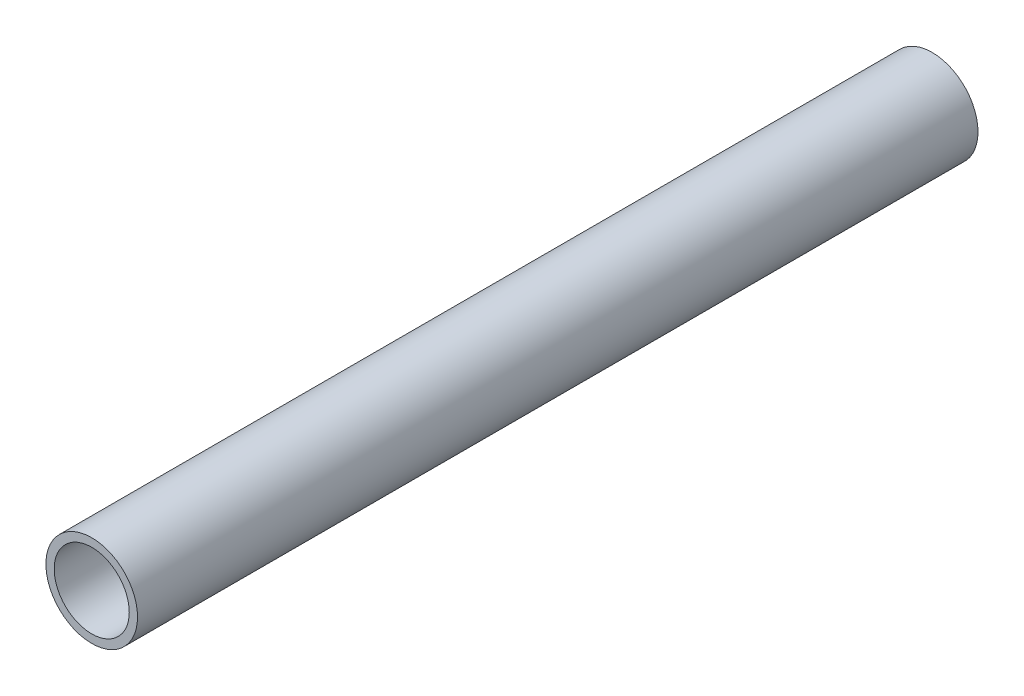
SolidWorks part; units mm, degrees
material "Thornel Mat VMA"
ref_plane "Płaszczyzna XY" through (0, 0, 0) normal (0, 0, 1) x (1, 0, 0)
ref_plane "Płaszczyzna XZ" through (0, 0, 0) normal (0, 1, 0) x (1, 0, 0)
ref_plane "Płaszczyzna YZ" through (0, 0, 0) normal (1, 0, 0) x (0, 0, -1)
sketch "Szkic1" plane through (0, 0, 0) normal (0, 0, 1) x (1, 0, 0)
  circle A0 centre (0, 0) radius 7.75
  circle A1 centre (0, 0) radius 6.35
  dimension "D1" = 15.5
  dimension "D2" = 12.7
extrude "Dodanie-wyciągnięcie1" add sketch "Szkic1" along normal blind 142.2
